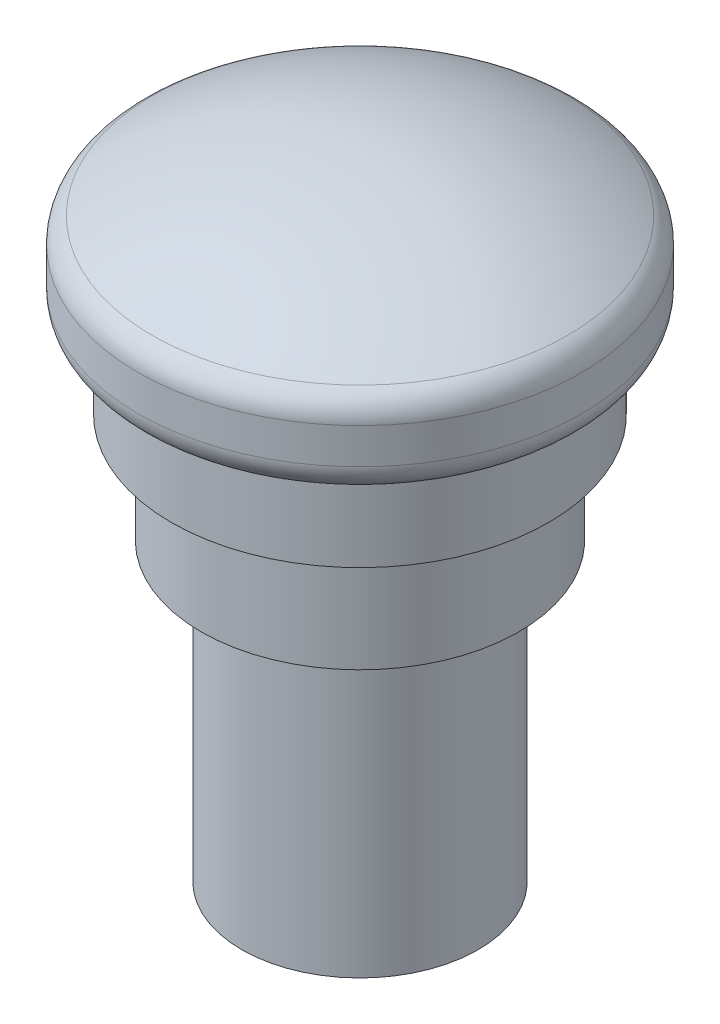
SolidWorks part; units mm, degrees
ref_plane "Front Plane" through (0, 0, 0) normal (0, 0, 1) x (1, 0, 0)
ref_plane "Top Plane" through (0, 0, 0) normal (0, 1, 0) x (1, 0, 0)
ref_plane "Right Plane" through (0, 0, 0) normal (1, 0, 0) x (0, 0, -1)
sketch "Sketch1" plane through (0, 0, 0) normal (1, 0, 0) x (0, 0, -1)
  line L0 (0, 0) -> (0, 43) construction
  line L1 (0, 43) -> (-17.9596, 43) construction
  line L2 (15, 38.4) -> (15, 32.9)
  line L3 (15, 32.9) -> (12.75, 32.9)
  line L4 (12.75, 32.9) -> (12.75, 27.4)
  line L5 (12.75, 27.4) -> (10.75, 27.4)
  line L6 (10.75, 27.4) -> (10.75, 20)
  line L7 (10.75, 20) -> (8, 20)
  line L8 (8, 20) -> (8, 0)
  line L9 (8, 0) -> (0, 0)
  line L10 (0, 43) -> (0, 0)
  arc A0 (0, 43) -> (15, 38.4) centre (0, 16.2435) cw
  dimension "D2" = 30
  dimension "D1" = 43
  dimension "D3" = 4.6
  dimension "D4" = 16
  dimension "D5" = 20
  dimension "D6" = 21.5
  dimension "D7" = 7.4
  dimension "D8" = 25.5
  dimension "D9" = 5.5
  dimension "D10" = 5.5
revolve "Revolve1" add sketch "Sketch1" angle 360 about L10
fillet "Fillet1" radius 2 2 edges at (0, 32.9, 15) (0, 38.4, 15)
